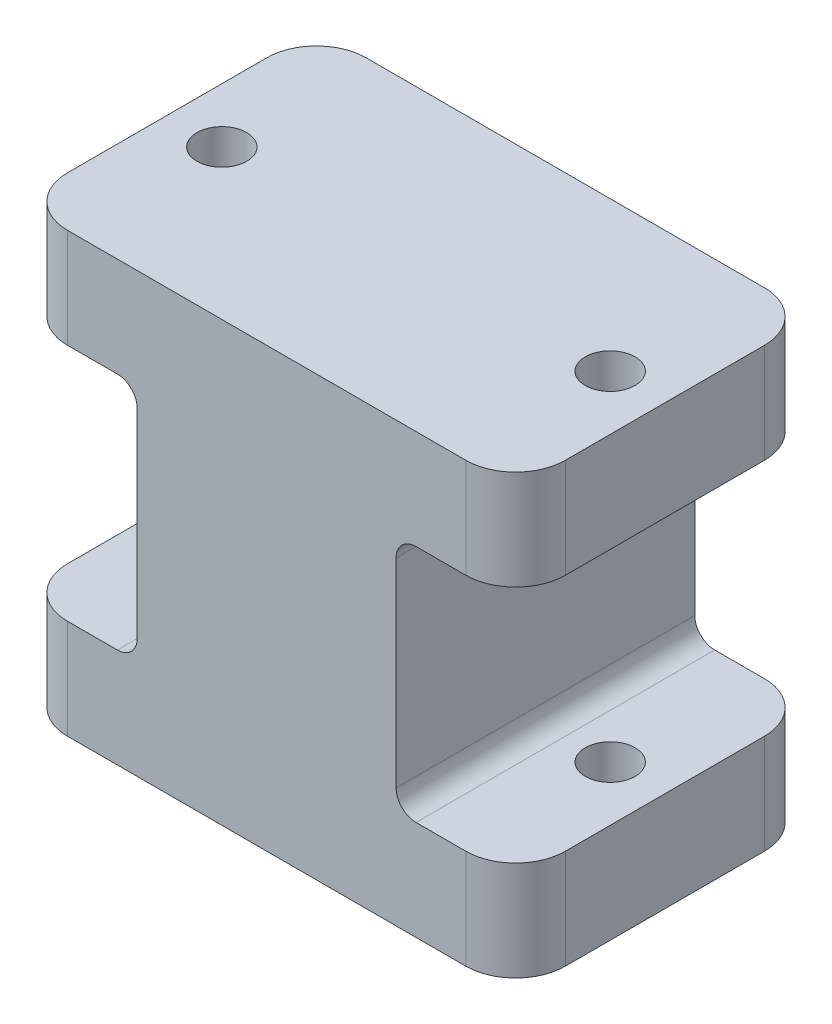
SolidWorks part; units mm, degrees
ref_plane "Front Plane" through (0, 0, 0) normal (0, 0, 1) x (1, 0, 0)
ref_plane "Top Plane" through (0, 0, 0) normal (0, 1, 0) x (1, 0, 0)
ref_plane "Right Plane" through (0, 0, 0) normal (1, 0, 0) x (0, 0, -1)
sketch "Sketch1" plane through (0, 0, 0) normal (0, 1, 0) x (1, 0, 0)
  line L0 (0, -55) -> (0, 55) construction
  line L1 (20, -15) -> (-20, -15)
  line L2 (25, -10) -> (25, 10)
  line L3 (20, 15) -> (-20, 15)
  line L4 (-25, -10) -> (-25, 10)
  line L5 (25, -15) -> (-25, 15) construction
  line L6 (25, 15) -> (-25, -15) construction
  circle A0 centre (-19.5, 0) radius 2.5
  circle A1 centre (19.5, 0) radius 2.5
  arc A2 (20, -15) -> (25, -10) centre (20, -10) ccw
  arc A3 (25, 10) -> (20, 15) centre (20, 10) ccw
  arc A4 (-20, -15) -> (-25, -10) centre (-20, -10) cw
  arc A5 (-20, 15) -> (-25, 10) centre (-20, 10) ccw
  point P0 (0, 0)
  dimension "D3" = 19.5
  dimension "D4" = 5
  dimension "D1" = 50
  dimension "D2" = 30
extrude "Boss-Extrude1" add sketch "Sketch1" along normal blind 44
sketch "Sketch2" plane through (-25, 0, 0) normal (-1, 0, 0) x (0, 0, 1)
  line L0 (-15, 44) -> (-15, 0) construction
  line L1 (15, 10) -> (-15, 10)
  line L2 (15, 10) -> (15, 34)
  line L3 (15, 34) -> (-15, 34)
  line L4 (-15, 10) -> (-15, 34)
  line L5 (15, 10) -> (-15, 34) construction
  line L6 (15, 34) -> (-15, 10) construction
  line L7 (15, 44) -> (15, 0) construction
  point P0 (0, 22)
  point P9 (15, 22)
  dimension "D1" = 24
  dimension "D2" = 0
extrude "Cut-Extrude1" cut sketch "Sketch2" against normal blind 12
mirror "Mirror1" about plane through (0, 0, 0) normal (1, 0, 0) of "Cut-Extrude1"
fillet "Fillet1" radius 2 4 edges at (13, 34, 0) (13, 10, 0) (-13, 10, 0) (-13, 34, 0)
